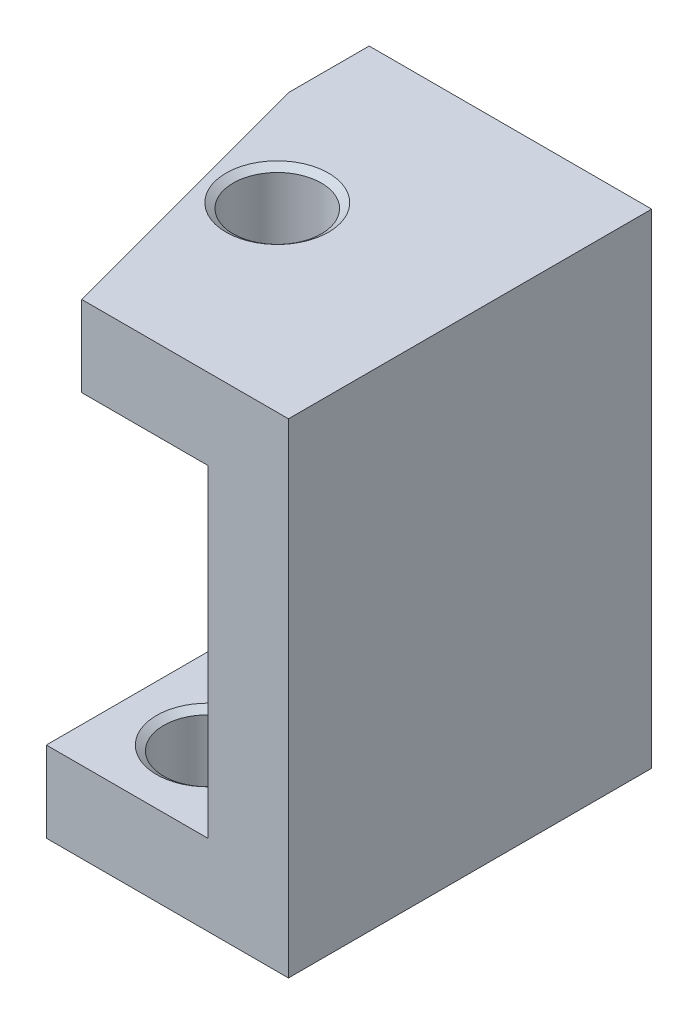
SolidWorks part; units mm, degrees
ref_plane "Спереди" through (0, 0, 0) normal (0, 0, 1) x (1, 0, 0)
ref_plane "Сверху" through (0, 0, 0) normal (0, 1, 0) x (1, 0, 0)
ref_plane "Справа" through (0, 0, 0) normal (1, 0, 0) x (0, 0, -1)
sketch "Эскиз1" plane through (0, 0, 0) normal (0, 0, 1) x (1, 0, 0)
  line L0 (2, 10) -> (23, 10)
  line L1 (0, 0) -> (25, 0)
  line L2 (0, 0) -> (0, 12)
  line L3 (0, 12) -> (25, 12)
  line L4 (25, 0) -> (25, 12)
  line L5 (23, 2) -> (23, 10)
  line L6 (2, 2) -> (23, 2)
  line L7 (2, 2) -> (2, 10)
  dimension "D1" = 12
  dimension "D2" = 25
  dimension "D3" = 2
extrude "Бобышка-Вытянуть1" add sketch "Эскиз1" along normal blind 9
sketch "Эскиз2" plane through (0, 0, 9) normal (0, 0, 1) x (1, 0, 0)
  line L0 (18, 12) -> (18, 6.1741)
  line L1 (25, 12) -> (0, 12) construction
  line L2 (18, 6.1741) -> (19, 6.1741)
  line L3 (19, 6.1741) -> (19, 0)
  line L4 (0, 0) -> (25, 0) construction
  line L5 (25, 0) -> (25, 12) construction
  line M1 (0, 12) -> (0, 0)
  line M2 (0, 0) -> (25, 0)
  line M4 (25, 12) -> (0, 12)
  line M5 (2, 2) -> (2, 10)
  line M6 (2, 10) -> (23, 10)
  line M8 (23, 2) -> (2, 2)
  dimension "D1" = 7
  dimension "D2" = 6
extrude "Вырез-Вытянуть1" cut sketch "Эскиз2" against normal through all contours L3 L0 M8 M5 M6 M4 M1 M2
chamfer "Фаска1" distance 7 angle 15 1 edges at (18, 11, 9)
hole_wizard "Отверстие обработанное метчиком #2-561" positions "Эскиз4" profile "Эскиз5" tap size "#2-56" standard "Ansi (в дюймах)" end condition up to next
sketch "Эскиз4" plane through (0, 0, 0) normal (0, -1, 0) x (1, 0, 0)
  line L0 (19, 0) -> (19, 9) construction
  line L1 (19, 9) -> (25, 9) construction
  line L2 (19, 0) -> (25, 0) construction
  point P0 (21, 2)
  point P1 (21, 7)
  dimension "D1" = 2
  dimension "D2" = 2
  dimension "D3" = 2
sketch "Эскиз5" plane through (21, 0, 2) normal (1, 0, 0) x (0, 0, -1)
  line L0 (0, 0) -> (0, 2)
  line L1 (0, 2) -> (1.27, 2)
  line L2 (1.0922, 1.8755) -> (1.0922, 0.1245)
  line L3 (1.0922, 0.1245) -> (1.27, 0)
  line L5 (1.27, 0) -> (0, 0)
  line L6 (-1.0922, 0.1245) -> (-1.27, 0) construction
  line L7 (1.27, 2) -> (1.0922, 1.8755)
  line L8 (-1.27, 2) -> (-1.0922, 1.8755) construction
  line L11 (0, -6.35) -> (0, 107.95) construction
  dimension "Диаметр резьбы" = 2.1844
  dimension "Глубина проходного сверла" = 2
  dimension "Диаметр передней зенковки" = 2.54
  dimension "Угол передней зенковки" = 110
  dimension "Диаметр задней зенковки" = 2.54
  dimension "Угол задней зенковки" = 110
hole_wizard "Отверстие обработанное метчиком #2-562" positions "Эскиз7" profile "Эскиз6" tap size "#2-56" standard "Ansi (в дюймах)" end condition up to next
sketch "Эскиз7" plane through (0, 12, 0) normal (0, 1, 0) x (-1, 0, 0)
  line L1 (-18, 2) -> (-19.8756, 9) construction
  line L3 (-25, 9) -> (-19.8756, 9) construction
  point P0 (-20.2228, 4.5)
  dimension "D1" = 1.5
  dimension "D2" = 4.5
sketch "Эскиз6" plane through (20.2228, 12, 4.5) normal (1, 0, 0) x (0, 0, 1)
  line L0 (0, 0) -> (0, 2)
  line L1 (0, 2) -> (1.27, 2)
  line L2 (1.0922, 1.8755) -> (1.0922, 0.1245)
  line L3 (1.0922, 0.1245) -> (1.27, 0)
  line L5 (1.27, 0) -> (0, 0)
  line L6 (-1.0922, 0.1245) -> (-1.27, 0) construction
  line L7 (1.27, 2) -> (1.0922, 1.8755)
  line L8 (-1.27, 2) -> (-1.0922, 1.8755) construction
  line L11 (0, -6.35) -> (0, 107.95) construction
  dimension "Диаметр резьбы" = 2.1844
  dimension "Глубина проходного сверла" = 2
  dimension "Диаметр передней зенковки" = 2.54
  dimension "Угол передней зенковки" = 110
  dimension "Диаметр задней зенковки" = 2.54
  dimension "Угол задней зенковки" = 110
